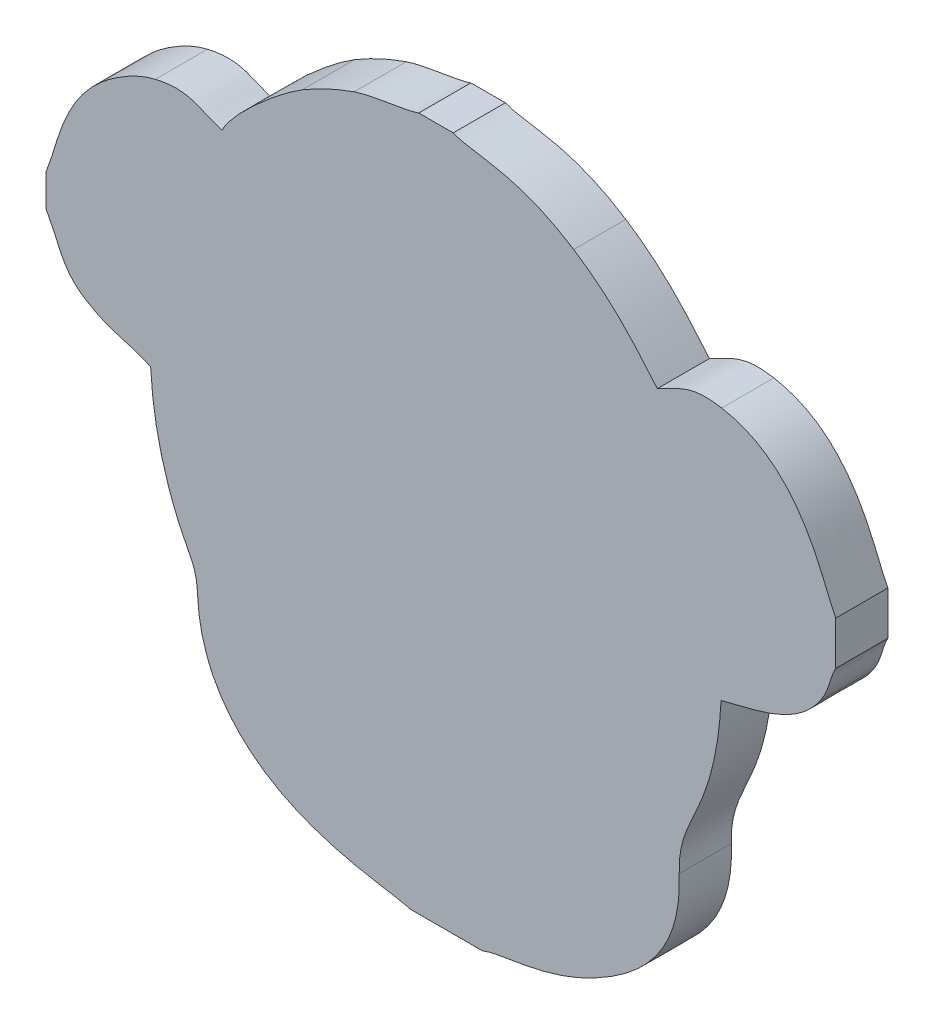
SolidWorks part; units mm, degrees
ref_plane "Front Plane" through (0, 0, 0) normal (0, 0, 1) x (1, 0, 0)
ref_plane "Top Plane" through (0, 0, 0) normal (0, 1, 0) x (1, 0, 0)
ref_plane "Right Plane" through (0, 0, 0) normal (1, 0, 0) x (0, 0, -1)
sketch "Model" plane through (0, 0, 0) normal (0, 0, 1) x (1, 0, 0)
  line L0 (55.1272, 105.2165) -> (55.1272, 103.3338)
  line L1 (76.0211, 78.9235) -> (80.2468, 78.9235)
  line L2 (100.5659, 103.1647) -> (100.5659, 105.6703)
  line L3 (78.5521, 118.8487) -> (76.5707, 118.8487)
  spline S0 degree 3 poles (55.1272, 103.3338) (55.9357, 101.875) (56.0272, 100.8916) (57.2517, 100.0613) knots 0.038462 0.038462 0.038462 0.038462 0.076923 0.076923 0.076923 0.076923
  spline S1 degree 3 poles (57.2517, 100.0613) (58.7272, 99.0608) (59.7559, 99.1354) (61.1406, 98.4843) knots 0.076923 0.076923 0.076923 0.076923 0.115385 0.115385 0.115385 0.115385
  spline S2 degree 3 poles (61.1406, 98.4843) (61.2643, 95.9602) (61.838, 93.6047) (62.7653, 91.5083) knots 0.115385 0.115385 0.115385 0.115385 0.153846 0.153846 0.153846 0.153846
  spline S3 degree 3 poles (62.7653, 91.5083) (63.3171, 90.261) (63.7888, 89.9265) (63.8434, 88.4315) knots 0.153846 0.153846 0.153846 0.153846 0.192308 0.192308 0.192308 0.192308
  spline S4 degree 3 poles (63.8434, 88.4315) (63.8899, 87.1583) (64.224, 85.8877) (64.7219, 84.8986) knots 0.192308 0.192308 0.192308 0.192308 0.230769 0.230769 0.230769 0.230769
  spline S5 degree 3 poles (64.7219, 84.8986) (67.4566, 79.4661) (74.7931, 79.4131) (76.0211, 78.9235) knots 0.230769 0.230769 0.230769 0.230769 0.269231 0.269231 0.269231 0.269231
  spline S6 degree 3 poles (80.2468, 78.9235) (81.4396, 79.4171) (83.7679, 79.2274) (86.7105, 80.8069) knots 0.307692 0.307692 0.307692 0.307692 0.346154 0.346154 0.346154 0.346154
  spline S7 degree 3 poles (86.7105, 80.8069) (89.8776, 82.5068) (91.6976, 84.7693) (91.5598, 88.4331) knots 0.346154 0.346154 0.346154 0.346154 0.384615 0.384615 0.384615 0.384615
  spline S8 degree 3 poles (91.5598, 88.4331) (91.4432, 91.536) (93.6274, 92.0439) (93.9689, 98.2668) knots 0.384615 0.384615 0.384615 0.384615 0.423077 0.423077 0.423077 0.423077
  spline S9 degree 3 poles (93.9689, 98.2668) (96.0863, 98.8396) (98.2608, 99.0994) (99.6714, 101.1074) knots 0.423077 0.423077 0.423077 0.423077 0.461538 0.461538 0.461538 0.461538
  spline S10 degree 3 poles (99.6714, 101.1074) (100.2485, 101.9289) (100.1784, 102.4641) (100.5659, 103.1647) knots 0.461538 0.461538 0.461538 0.461538 0.5 0.5 0.5 0.5
  spline S11 degree 3 poles (100.5659, 105.6703) (99.7223, 107.2591) (98.5859, 112.0519) (94.0061, 112.8642) knots 0.538462 0.538462 0.538462 0.538462 0.576923 0.576923 0.576923 0.576923
  spline S12 degree 3 poles (94.0061, 112.8642) (92.18, 113.1882) (91.4848, 112.5304) (90.2994, 111.974) knots 0.576923 0.576923 0.576923 0.576923 0.615385 0.615385 0.615385 0.615385
  spline S13 degree 3 poles (90.2994, 111.974) (88.7995, 113.7706) (87.5152, 115.1976) (85.4874, 116.5045) knots 0.615385 0.615385 0.615385 0.615385 0.653846 0.653846 0.653846 0.653846
  spline S14 degree 3 poles (85.4874, 116.5045) (82.1232, 118.6728) (79.9482, 118.2978) (78.5521, 118.8487) knots 0.653846 0.653846 0.653846 0.653846 0.692308 0.692308 0.692308 0.692308
  spline S15 degree 3 poles (76.5707, 118.8487) (75.9147, 118.5898) (73.949, 118.4167) (72.8515, 118.0451) knots 0.730769 0.730769 0.730769 0.730769 0.769231 0.769231 0.769231 0.769231
  spline S16 degree 3 poles (72.8515, 118.0451) (71.807, 117.6915) (70.6758, 117.1447) (69.865, 116.6538) knots 0.769231 0.769231 0.769231 0.769231 0.807692 0.807692 0.807692 0.807692
  spline S17 degree 3 poles (69.865, 116.6538) (68.5207, 115.84) (65.7355, 113.4696) (65.2526, 112.3186) knots 0.807692 0.807692 0.807692 0.807692 0.846154 0.846154 0.846154 0.846154
  spline S18 degree 3 poles (65.2526, 112.3186) (63.7751, 112.8048) (63.3732, 113.3887) (61.4119, 112.9491) knots 0.846154 0.846154 0.846154 0.846154 0.884615 0.884615 0.884615 0.884615
  spline S19 degree 3 poles (61.4119, 112.9491) (60.2523, 112.6892) (59.0201, 111.8593) (58.3253, 111.2712) knots 0.884615 0.884615 0.884615 0.884615 0.923077 0.923077 0.923077 0.923077
  spline S20 degree 3 poles (58.3253, 111.2712) (56.0021, 109.3047) (55.7198, 106.5647) (55.1272, 105.2165) knots 0.923077 0.923077 0.923077 0.923077 1 1 1 1
extrude "Boss-Extrude1" add sketch "Model" along normal blind 3
